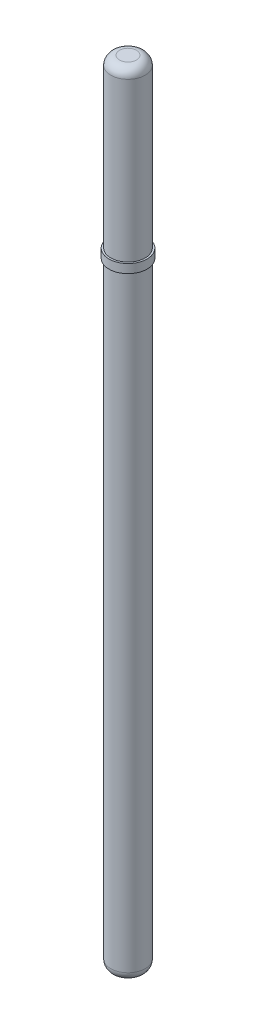
SolidWorks part; units mm, degrees
ref_plane "前视基准面" through (0, 0, 0) normal (0, 0, 1) x (1, 0, 0)
ref_plane "上视基准面" through (0, 0, 0) normal (0, 1, 0) x (1, 0, 0)
ref_plane "右视基准面" through (0, 0, 0) normal (1, 0, 0) x (0, 0, -1)
sketch "草图1" plane through (0, 0, 0) normal (0, 1, 0) x (1, 0, 0)
  circle A0 centre (0, 0) radius 0.98
  dimension "D1" = 1.96
extrude "凸台-拉伸1" add sketch "草图1" along normal blind 45
fillet "圆角1" radius 0.5 2 edges at (0, 0, 0.98) (0, 45, 0.98)
ref_plane "基准面1" through (0, 35.5, 0) normal (0, 1, 0) x (1, 0, 0)
sketch "草图2" plane through (0, 35.5, 0) normal (0, 1, 0) x (1, 0, 0)
  circle A0 centre (0, 0) radius 0.98
extrude "拉伸-薄壁1" add sketch "草图2" against normal blind 0.5 thin
